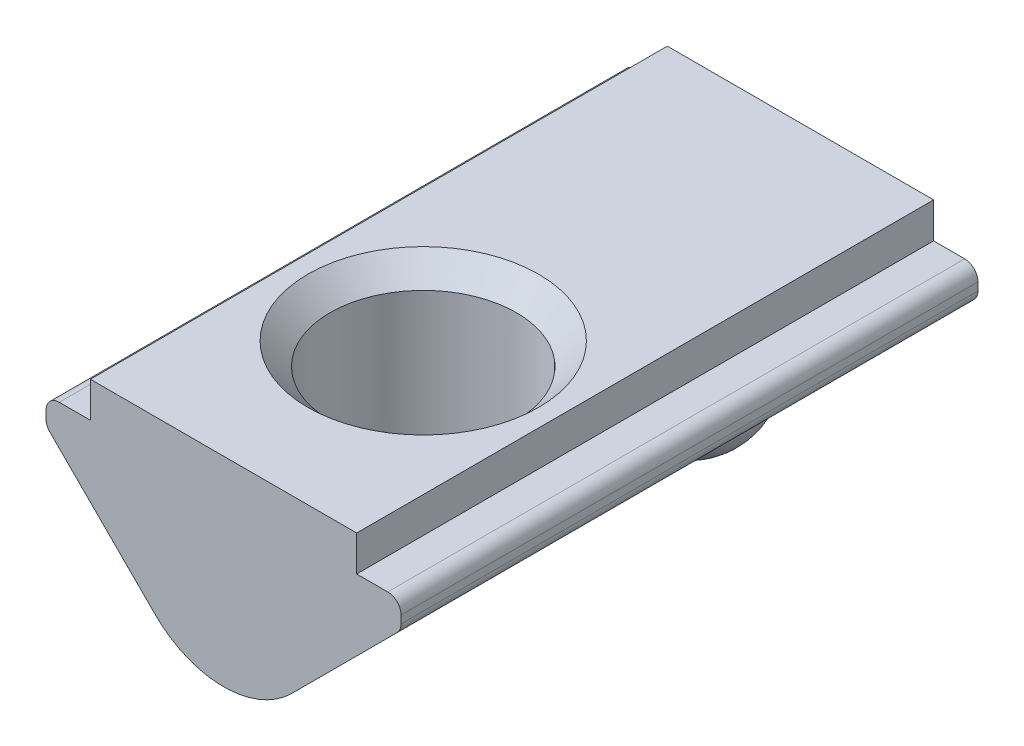
SolidWorks part; units mm, degrees
ref_plane "Спереди" through (0, 0, 0) normal (0, 0, 1) x (1, 0, 0)
ref_plane "Сверху" through (0, 0, 0) normal (0, 1, 0) x (1, 0, 0)
ref_plane "Справа" through (0, 0, 0) normal (1, 0, 0) x (0, 0, -1)
sketch "Эскиз1" plane through (0, 0, 0) normal (0, 0, 1) x (1, 0, 0)
  line L0 (-3, 0) -> (3, 0)
  line L2 (4, -1.4) -> (1.5364, -3.8636)
  line L3 (-1.5364, -3.8636) -> (-4, -1.4)
  line L5 (-3, 0) -> (-3, -0.8)
  line L6 (-3, -0.8) -> (-4, -0.8)
  line L7 (-4, -0.8) -> (-4, -1.4)
  line L8 (3, 0) -> (3, -0.8)
  line L9 (3, -0.8) -> (4, -0.8)
  line L10 (4, -0.8) -> (4, -1.4)
  arc A0 (1.5364, -3.8636) -> (-1.5364, -3.8636) centre (0, -2.3272) cw
  point P4 (0, 0)
  point P6 (-4, -1.8735)
  point P9 (3.8192, -0.8723)
  point P16 (4, -0.8)
  point P17 (4, -0.8)
  point P18 (4, -1.7542)
  point P19 (-2.142, -3.1262)
  dimension "D1" = 6
  dimension "D2" = 8
  dimension "D3" = 0.8
  dimension "D4" = 45
  dimension "D5" = 0.6
  dimension "D6" = 4.5
extrude "Бобышка-Вытянуть1" add sketch "Эскиз1" along normal mid plane 13
hole_wizard "Отверстие обработанное метчиком M51" positions "Эскиз2" profile "Эскиз4" tap size "M5" standard "ISO" end condition through all
sketch "Эскиз2" plane through (0, 0, 0) normal (0, 1, 0) x (1, 0, 0)
  line L0 (3, -6.5) -> (-3, -6.5) construction
  point P0 (0, -2)
  dimension "D1" = 4.5
sketch "Эскиз4" plane through (0, 0, 2) normal (1, 0, 0) x (0, 0, 1)
  line L0 (0, 0) -> (0, 4.5)
  line L1 (0, 4.5) -> (2.1, 4.5)
  line L2 (2.1, 4.5) -> (2.1, 0.5)
  line L3 (2.1, 0.5) -> (2.6, 0)
  line L5 (2.6, 0) -> (0, 0)
  line L6 (-2.1, 0.5) -> (-2.6, 0) construction
  line L11 (0, -6.35) -> (0, 107.95) construction
  dimension "Диаметр проходного сверла" = 4.2
  dimension "Глубина проходного сверла" = 4.5
  dimension "Диаметр передней зенковки" = 5.2
  dimension "Угол передней зенковки" = 90
cosmetic thread "Отверстие резьбы1" parameters "D2"=5
sketch "Эскиз5" plane through (0, 0, 0) normal (1, 0, 0) x (0, 0, -1)
  line L0 (-6.5, 0) -> (6.5, 0) construction
  line L1 (4, -2) -> (4, -5) construction
  line L2 (6.5, -3.8636) -> (6.5, -1.4) construction
  line L3 (4, -2) -> (4, -5)
  arc A0 (4, -2) -> (4, -5) centre (4, -3.5) ccw
  point P3 (0, 0)
  dimension "D3" = 1.5
  dimension "D1" = 5
  dimension "D2" = 2.5
revolve "Повернуть1" add sketch "Эскиз5" angle 360 about L1
fillet "Скругление1" radius 0.3 4 edges at (4, -1.4, 0) (4, -0.8, 0) (-4, -0.8, 0) (-4, -1.4, 0)
